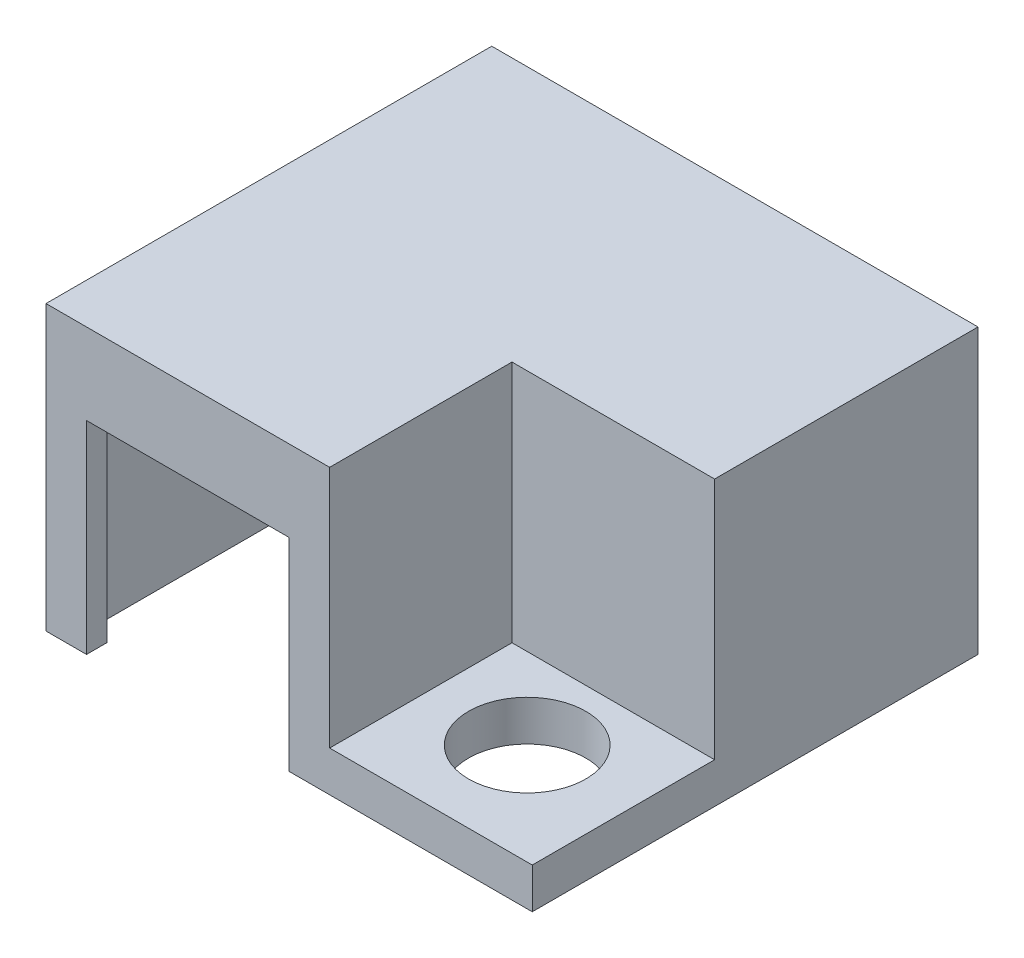
SolidWorks part; units mm, degrees
ref_plane "Plan de face" through (0, 0, 0) normal (0, 0, 1) x (1, 0, 0)
ref_plane "Plan de dessus" through (0, 0, 0) normal (0, 1, 0) x (1, 0, 0)
ref_plane "Plan de droite" through (0, 0, 0) normal (1, 0, 0) x (0, 0, -1)
sketch "Esquisse1" plane through (0, 0, 0) normal (0, 1, 0) x (1, 0, 0)
  line L1 (0, 0) -> (24, 0)
  line L2 (0, 0) -> (0, 22)
  line L3 (0, 22) -> (24, 22)
  line L4 (24, 0) -> (24, 22)
  dimension "D1" = 24
  dimension "D2" = 22
extrude "Boss.-Extru.1" add sketch "Esquisse1" along normal blind 2
sketch "Esquisse2" plane through (0, 2, 0) normal (0, 1, 0) x (1, 0, 0)
  line L0 (0, 22) -> (1, 22) construction
  line L1 (24, 22) -> (0, 22) construction
  line L2 (1, 22) -> (1, 21) construction
  line L3 (1, 21) -> (23, 21) construction
  line L4 (1, 21) -> (23, 21)
  line L5 (23, 21) -> (23, 10)
  line L6 (23, 10) -> (13, 10)
  line L7 (13, 10) -> (13, 1)
  line L8 (13, 1) -> (1, 1)
  line L9 (1, 1) -> (1, 21)
  dimension "D1" = 1
  dimension "D2" = 1
  dimension "D3" = 22
  dimension "D4" = 11
  dimension "D5" = 10
  dimension "D6" = 9
extrude "Enlèv. mat.-Extru.1" cut sketch "Esquisse2" against normal blind 2
sketch "Esquisse3" plane through (0, 2, 0) normal (0, 1, 0) x (1, 0, 0)
  line L0 (24, 0) -> (20.5, 0) construction
  line L1 (0, 0) -> (24, 0) construction
  line L2 (20.5, 0) -> (20.5, 5) construction
  line L3 (24, 0) -> (17, 0) construction
  line L4 (17, 0) -> (17, 5) construction
  line L5 (17, 5) -> (20.5, 5) construction
  circle A0 centre (18.75, 5) radius 1.75
  dimension "D1" = 3.5
  dimension "D2" = 5
  dimension "D3" = 7
extrude "Enlèv. mat.-Extru.2" cut sketch "Esquisse3" against normal blind 2
sketch "Esquisse4" plane through (0, 2, 0) normal (0, 1, 0) x (1, 0, 0)
  circle A0 centre (18.75, 5) radius 2.8947
extrude "Enlèv. mat.-Extru.3" cut sketch "Esquisse4" against normal blind 2
sketch "Esquisse5" plane through (0, 2, 0) normal (0, 1, 0) x (1, 0, 0)
  line L0 (23, 10) -> (23, 9) construction
  line L1 (13, 1) -> (14, 1) construction
  line L2 (14, 1) -> (14, 9) construction
  line L3 (23, 9) -> (14, 9) construction
  line L4 (14, 9) -> (14, 0)
  line L5 (0, 0) -> (24, 0) construction
  line L6 (14, 0) -> (0, 0)
  line L7 (0, 0) -> (0, 22)
  line L8 (0, 22) -> (24, 22)
  line L9 (24, 22) -> (24, 9)
  line L10 (24, 0) -> (24, 22) construction
  line L11 (24, 9) -> (14, 9)
  line L12 (1, 21) -> (23, 21)
  line L13 (23, 21) -> (23, 10)
  line L14 (23, 10) -> (13, 10)
  line L15 (13, 10) -> (13, 1)
  line L16 (13, 1) -> (1, 1)
  line L17 (1, 1) -> (1, 21)
  line L18 (1, 21) -> (0.9732, 21.0032)
  dimension "D1" = 1
  dimension "D2" = 1
extrude "Boss.-Extru.2" add sketch "Esquisse5" along normal blind 10
sketch "Esquisse6" plane through (0, 0, 0) normal (0, 0, 1) x (1, 0, 0)
  line L0 (0, 0) -> (2, 0) construction
  line L1 (0, 0) -> (24, 0) construction
  line L2 (14, 2) -> (14, 0) construction
  line L3 (14, 0) -> (12, 0) construction
  line L5 (2, 0) -> (12, 0)
  line L6 (2, 0) -> (2, 10)
  line L7 (2, 10) -> (12, 10)
  line L8 (12, 0) -> (12, 10)
  dimension "D1" = 2
  dimension "D2" = 10
extrude "Enlèv. mat.-Extru.4" cut sketch "Esquisse6" against normal blind 10
sketch "Esquisse8" plane through (0, 12, 0) normal (0, 1, 0) x (1, 0, 0)
  line L0 (0, 0) -> (0, 22)
  line L1 (0, 22) -> (24, 22)
  line L2 (24, 22) -> (24, 9)
  line L3 (24, 9) -> (14, 9)
  line L4 (14, 9) -> (14, 0)
  line L5 (14, 0) -> (0, 0)
extrude "Boss.-Extru.3" add sketch "Esquisse8" along normal blind 2
